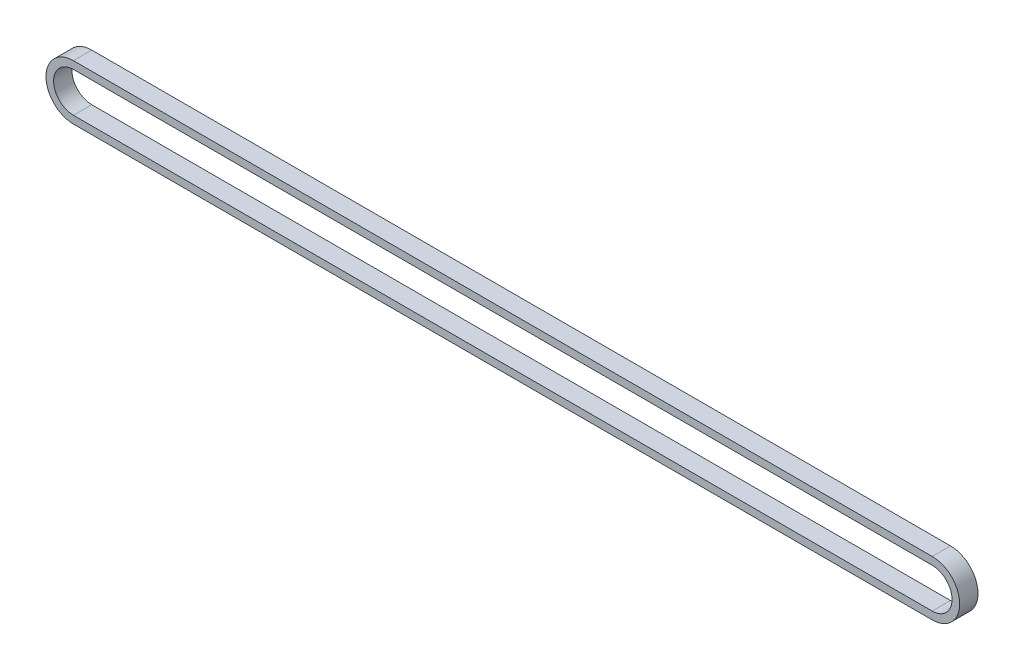
SolidWorks part; units mm, degrees
ref_plane "Front Plane" through (0, 0, 0) normal (0, 0, 1) x (1, 0, 0)
ref_plane "Top Plane" through (0, 0, 0) normal (0, 1, 0) x (1, 0, 0)
ref_plane "Right Plane" through (0, 0, 0) normal (1, 0, 0) x (0, 0, -1)
sketch "Sketch2" plane through (0, 0, 0) normal (0, 0, 1) x (1, 0, 0)
  line L5 (-140.6652, 0) -> (140.6652, 0) construction
  line L6 (-140.6652, 6.5) -> (140.6652, 6.5)
  line L10 (-140.6652, -6.5) -> (140.6652, -6.5)
  line L11 (-140.6652, 9) -> (140.6652, 9)
  line L12 (-140.6652, -9) -> (140.6652, -9)
  arc A3 (-140.6652, 6.5) -> (-140.6652, -6.5) centre (-140.6652, 0) ccw
  arc A7 (140.6652, -6.5) -> (140.6652, 6.5) centre (140.6652, 0) ccw
  arc A8 (140.6652, -9) -> (140.6652, 9) centre (140.6652, 0) ccw
  arc A9 (-140.6652, 9) -> (-140.6652, -9) centre (-140.6652, 0) ccw
  point P2 (0, 0)
  dimension "D3" = 2.5
  dimension "D1" = 281.3304
  dimension "D2" = 13
extrude "Boss-Extrude1" add sketch "Sketch2" along normal blind 6
